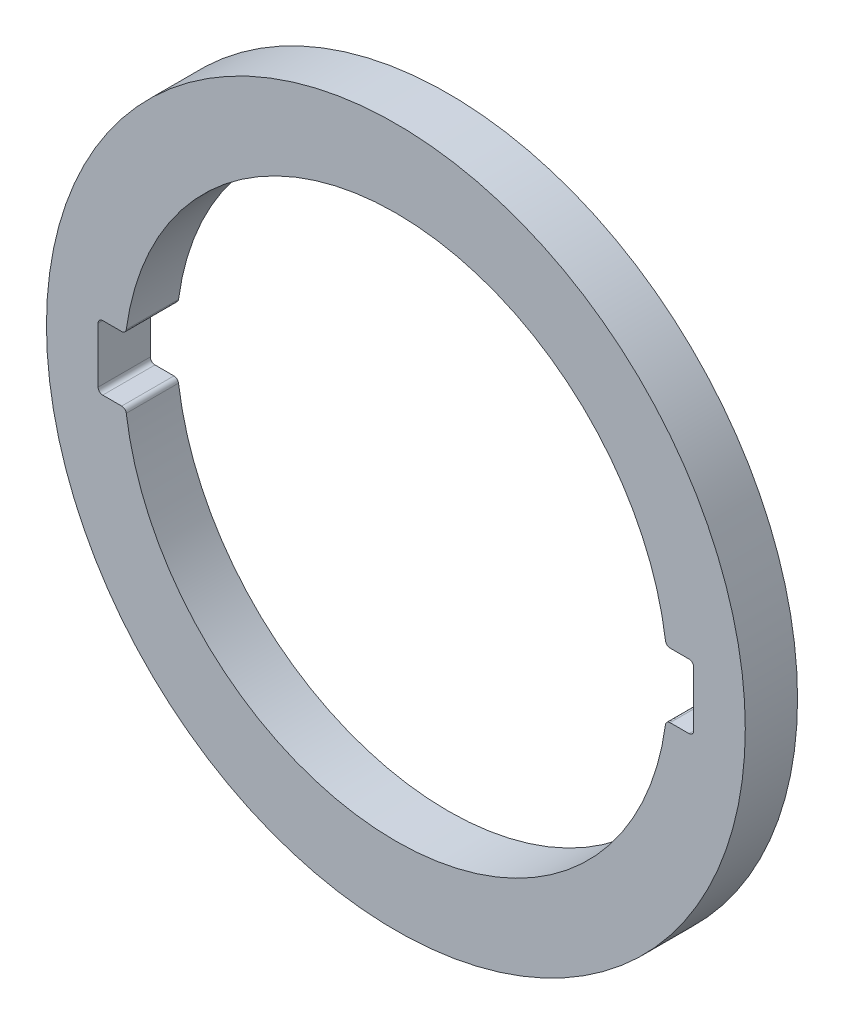
SolidWorks part; units mm, degrees
ref_plane "Ön Düzlem" through (0, 0, 0) normal (0, 0, 1) x (1, 0, 0)
ref_plane "Üst Düzlem" through (0, 0, 0) normal (0, 1, 0) x (1, 0, 0)
ref_plane "Sağ Düzlem" through (0, 0, 0) normal (1, 0, 0) x (0, 0, -1)
sketch "Çizim1" plane through (0, 0, 0) normal (0, 0, 1) x (1, 0, 0)
  line L0 (594.0985, 947.5) -> (-1175.9015, 947.5) construction
  line L1 (-290.9015, 62.5) -> (-290.9015, 1832.5) construction
  line L4 (587.8477, 842.5) -> (662.8477, 842.5)
  line L5 (677.8477, 857.5) -> (677.8477, 1037.5)
  line L6 (662.8477, 1052.5) -> (587.8477, 1052.5)
  line L7 (-1169.6506, 842.5) -> (-1244.6506, 842.5)
  line L8 (-1259.6506, 857.5) -> (-1259.6506, 1037.5)
  line L9 (-1244.6506, 1052.5) -> (-1169.6506, 1052.5)
  circle A0 centre (-290.9015, 947.5) radius 1136.7799
  arc A1 (-1169.6506, 842.5) -> (587.8477, 842.5) centre (-290.9015, 947.5) ccw
  arc A2 (662.8477, 842.5) -> (677.8477, 857.5) centre (662.8477, 857.5) ccw
  arc A3 (677.8477, 1037.5) -> (662.8477, 1052.5) centre (662.8477, 1037.5) ccw
  arc A4 (-1244.6506, 842.5) -> (-1259.6506, 857.5) centre (-1244.6506, 857.5) cw
  arc A5 (-1259.6506, 1037.5) -> (-1244.6506, 1052.5) centre (-1244.6506, 1037.5) cw
  arc A6 (587.8477, 1052.5) -> (-1169.6506, 1052.5) centre (-290.9015, 947.5) ccw
  point P17 (677.8477, 842.5)
  dimension "D1" = 1770
  dimension "D5" = 15
  dimension "D4" = 90
extrude "Yükseklik-Ekstrüzyon1" add sketch "Çizim1" along normal blind 30 and the other way blind 140
fillet "Radyus1" radius 15 4 edges at (-1169.6506, 842.5, -55) (-1169.6506, 1052.5, -55) (587.8477, 842.5, -55) (587.8477, 1052.5, -55)
